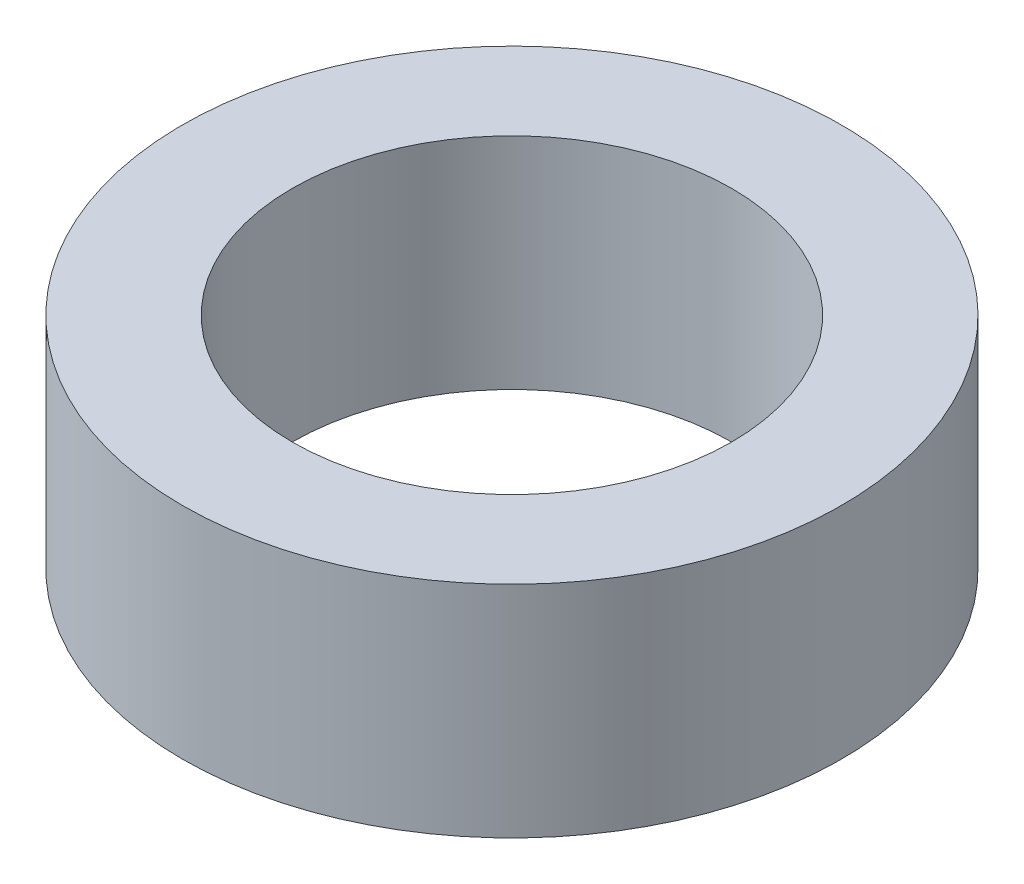
SolidWorks part; units mm, degrees
ref_plane "Front Plane" through (0, 0, 0) normal (0, 0, 1) x (1, 0, 0)
ref_plane "Top Plane" through (0, 0, 0) normal (0, 1, 0) x (1, 0, 0)
ref_plane "Right Plane" through (0, 0, 0) normal (1, 0, 0) x (0, 0, -1)
sketch "Sketch1" plane through (0, 0, 0) normal (0, 1, 0) x (1, 0, 0)
  circle A0 centre (0, 0) radius 3.175
  circle A1 centre (0, 0) radius 4.7625
  dimension "D1" = 6.35
  dimension "D2" = 9.525
extrude "Boss-Extrude3" add sketch "Sketch1" along normal blind 3.175
